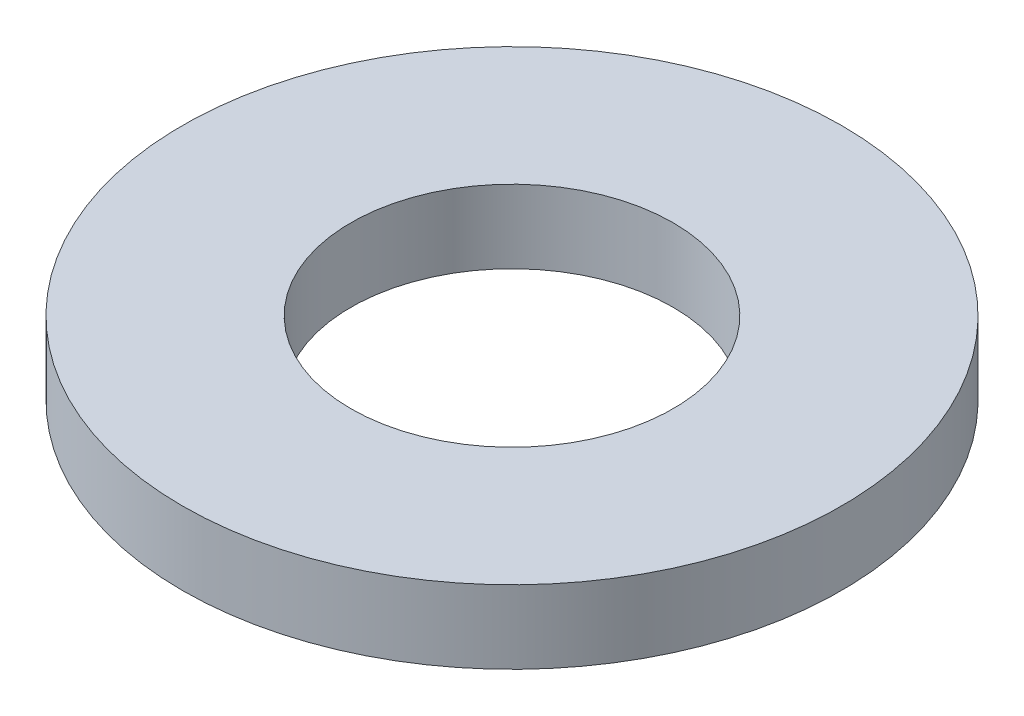
SolidWorks part; units mm, degrees
material "uhlíková ocel 7850"
ref_plane "Přední rovina" through (0, 0, 0) normal (0, 0, 1) x (1, 0, 0)
ref_plane "Horní rovina" through (0, 0, 0) normal (0, 1, 0) x (1, 0, 0)
ref_plane "Pravá rovina" through (0, 0, 0) normal (1, 0, 0) x (0, 0, -1)
sketch "Skica1" plane through (0, 0, 0) normal (0, 1, 0) x (1, 0, 0)
  circle A0 centre (0, 0) radius 2.25
  circle A1 centre (0, 0) radius 1.1
  dimension "D1" = 2.2
  dimension "D2" = 4.5
extrude "Přidat vysunutím1" add sketch "Skica1" along normal blind 0.5
